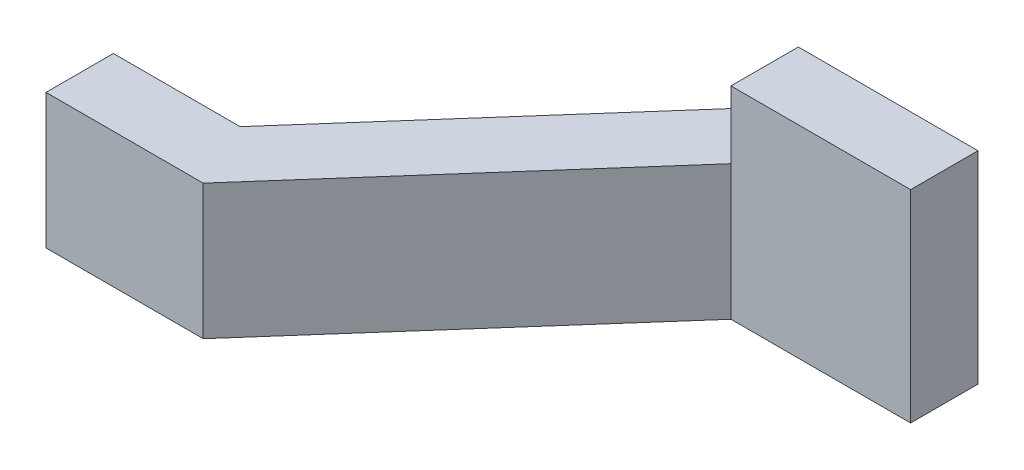
SolidWorks part; units mm, degrees
ref_plane "Front Plane" through (0, 0, 0) normal (0, 0, 1) x (1, 0, 0)
ref_plane "Top Plane" through (0, 0, 0) normal (0, 1, 0) x (1, 0, 0)
ref_plane "Right Plane" through (0, 0, 0) normal (1, 0, 0) x (0, 0, -1)
sketch "Sketch1" plane through (0, 0, 0) normal (0, 1, 0) x (1, 0, 0)
  line L0 (0, 0) -> (0.889, 0)
  line L1 (0.889, 0) -> (2.286, 1.5875)
  line L2 (2.286, 1.5875) -> (3.302, 1.5875)
  line L3 (3.302, 1.5875) -> (3.302, 1.9685)
  line L4 (0, 0) -> (0, 0.381)
  line L5 (0.7168, 0.381) -> (2.1138, 1.9685)
  line L6 (1.6109, 0.8204) -> (1.3249, 1.0721) construction
  line L7 (0, 0.381) -> (0.7168, 0.381)
  line L8 (3.302, 1.9685) -> (2.1138, 1.9685)
  dimension "D1" = 3.302
  dimension "D2" = 0.381
  dimension "D3" = 0.889
  dimension "D4" = 1.016
  dimension "D5" = 1.9685
extrude "Boss-Extrude1" add sketch "Sketch1" along normal mid plane 1.524
sketch "Sketch2" plane through (0, 0, -1.9685) normal (0, 0, -1) x (-1, 0, 0)
  line L0 (-2.286, 0.762) -> (-2.286, -0.762) construction
  line L1 (0, 0.762) -> (-2.286, 0.762)
  line L2 (0, 0.762) -> (0, 0.381)
  line L3 (0, 0.381) -> (-2.286, 0.381)
  line L4 (-2.286, 0.762) -> (-2.286, 0.381)
  line L6 (0.8071, 0) -> (-0.8071, 0) construction
  dimension "D1" = 0.381
extrude "Cut-Extrude1" cut sketch "Sketch2" against normal through all
mirror "Mirror1" about plane through (0, 0, 0) normal (0, 1, 0) of "Cut-Extrude1"
ref_plane "Plane1" through (0, 0, -1.778) normal (0, 0, -1) x (-1, 0, 0)
sketch "Sketch3" plane through (0, 0, -1.9685) normal (0, 0, -1) x (-1, 0, 0)
  line L1 (-3.302, -0.762) -> (-2.286, -0.762)
  line L2 (-3.302, -0.762) -> (-3.302, -0.381)
  line L3 (-3.302, -0.381) -> (-2.286, -0.381)
  line L4 (-2.286, -0.762) -> (-2.286, -0.381)
extrude "Cut-Extrude2" cut sketch "Sketch3" against normal through all
